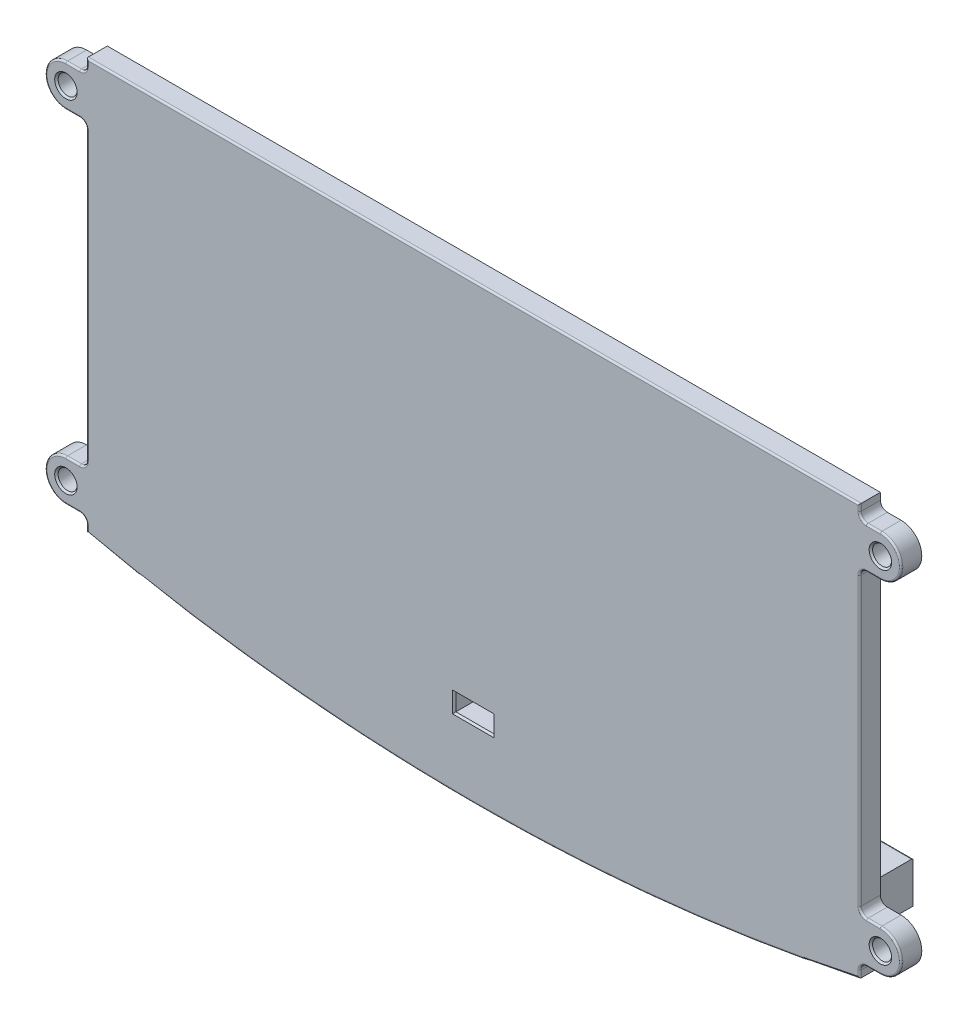
SolidWorks part; units mm, degrees
ref_plane "Front Plane" through (0, 0, 0) normal (0, 0, 1) x (1, 0, 0)
ref_plane "Top Plane" through (0, 0, 0) normal (0, 1, 0) x (1, 0, 0)
ref_plane "Right Plane" through (0, 0, 0) normal (1, 0, 0) x (0, 0, -1)
sketch "Sketch1" plane through (0, 0, 0) normal (0, 0, 1) x (1, 0, 0)
  line L5 (-56, 3) -> (56, 3)
  line L7 (56, 3) -> (56, 2)
  line L8 (57, 1) -> (59, 1)
  line L9 (59, -5) -> (57, -5)
  line L10 (56, -6) -> (56, -47.54)
  line L11 (57, -48.54) -> (59, -48.54)
  line L12 (59, -54.54) -> (57, -54.54)
  line L13 (56, -55.54) -> (56, -56.54)
  line L14 (-56, -56.54) -> (-56, -55.54)
  line L15 (-57, -54.54) -> (-59, -54.54)
  line L16 (-59, -48.54) -> (-57, -48.54)
  line L17 (-56, -47.54) -> (-56, -6)
  line L18 (-57, -5) -> (-59, -5)
  line L19 (-59, 1) -> (-57, 1)
  line L20 (-56, 2) -> (-56, 3)
  arc A13 (56, 2) -> (57, 1) centre (57, 2) ccw
  arc A14 (59, 1) -> (59, -5) centre (59, -2) cw
  arc A15 (57, -5) -> (56, -6) centre (57, -6) ccw
  arc A16 (56, -47.54) -> (57, -48.54) centre (57, -47.54) ccw construction
  arc A17 (56, -47.54) -> (57, -48.54) centre (57, -47.54) ccw
  arc A18 (59, -48.54) -> (59, -54.54) centre (59, -51.54) cw
  arc A20 (57, -54.54) -> (56, -55.54) centre (57, -55.54) ccw
  arc A21 (-56, -55.54) -> (-57, -54.54) centre (-57, -55.54) ccw
  arc A23 (-59, -54.54) -> (-59, -48.54) centre (-59, -51.54) cw
  arc A24 (-57, -48.54) -> (-56, -47.54) centre (-57, -47.54) ccw
  arc A25 (-56, -6) -> (-57, -5) centre (-57, -6) ccw
  arc A26 (-59, -5) -> (-59, 1) centre (-59, -2) cw
  arc A27 (-57, 1) -> (-56, 2) centre (-57, 2) ccw
  arc A29 (-56, -56.54) -> (56, -56.54) centre (0, 203.2465) ccw
  circle A30 centre (-59, -2) radius 1.375
  circle A31 centre (-59, -51.54) radius 1.375
  circle A32 centre (59, -51.54) radius 1.375
  circle A34 centre (59, -2) radius 1.375
  arc A35 (53, -57.1686) -> (56, -56.54) centre (0, 203.2465) ccw construction
  dimension "D1" = 2.75
extrude "Boss-Extrude1" add sketch "Sketch1" along normal blind 3
sketch "Sketch2" plane through (0, 0, 0) normal (0, 0, -1) x (-1, 0, 0)
  line L1 (54.5, -33) -> (-54.5, -33)
  line L2 (54.5, -33) -> (54.5, -30)
  line L3 (54.5, -30) -> (-54.5, -30)
  line L4 (-54.5, -33) -> (-54.5, -30)
extrude "Cut-Extrude1" cut sketch "Sketch2" against normal blind 1.5
chamfer "Chamfer1" distance 0.25 angle 45 4 edges at (60.375, -2, 3) (60.375, -51.54, 3) (-57.625, -51.54, 3) (-57.625, -2, 3)
fillet "Fillet1" radius 0.25 28 edges at (56, 2.5, 3) (56.2929, 1.2929, 3) (58, 1, 3) (62, -2, 3) (58, -5, 3) (56.2929, -5.2929, 3) (56, -26.77, 3) (56.2929, -48.2471, 3) (58, -48.54, 3) (62, -51.54, 3) (58, -54.54, 3) (56.2929, -54.8329, 3) (56, -56.04, 3) (-56, -56.04, 3) (0, -62.5072, 3) (-56.2929, -54.8329, 3) (-58, -54.54, 3) (-62, -51.54, 3) (-58, -48.54, 3) (-56.2929, -48.2471, 3) (-56, -26.77, 3) (-56.2929, -5.2929, 3) (-58, -5, 3) (-62, -2, 3) (-58, 1, 3) (-56.2929, 1.2929, 3) (-56, 2.5, 3) (0, 3, 3)
sketch "Sketch3" plane through (0, 0, 0) normal (0, 0, -1) x (-1, 0, 0)
  line L0 (53, -54.54) -> (51, -54.54) construction
  line L1 (52.75, -54.54) -> (-52.75, -54.54)
  line L2 (52.75, -54.54) -> (52.75, -48.54)
  line L3 (52.75, -48.54) -> (-52.75, -48.54)
  line L4 (-52.75, -54.54) -> (-52.75, -48.54)
  line L5 (-53, -33) -> (-53, -50.54) construction
  line L6 (53, -50.54) -> (53, -33) construction
  dimension "D1" = 0.25
  dimension "D2" = 0.25
  dimension "D3" = 6
extrude "Boss-Extrude2" add sketch "Sketch3" along normal blind 8
sketch "Sketch4" plane through (0, -54.54, 0) normal (0, -1, 0) x (1, 0, 0)
  line L0 (52.75, 0) -> (-52.75, 0) construction
  circle A0 centre (0, -3.25) radius 1.75
  point P4 (-3.4689, -3.25)
  dimension "D2" = 3.5
  dimension "D1" = 3.25
extrude "Cut-Extrude2" cut sketch "Sketch4" against normal through all
ref_plane "Plane1" through (0, -52.54, 0) normal (0, -1, 0) x (-1, 0, 0)
sketch "Sketch6" plane through (0, -52.54, 0) normal (0, -1, 0) x (-1, 0, 0)
  line L0 (2.75, 1.6623) -> (2.75, -3)
  line L1 (0, 6.4254) -> (-2.75, 4.8377)
  line L2 (-2.75, 4.8377) -> (-2.75, 1.6623)
  line L3 (-2.75, 1.6623) -> (-1.375, 0.8684) construction
  line L4 (1.375, 0.8684) -> (2.75, 1.6623) construction
  line L5 (2.75, 1.6623) -> (2.75, 4.8377)
  line L6 (2.75, 4.8377) -> (0, 6.4254)
  line L7 (-55.75, -3) -> (55.75, -3) construction
  line L8 (2.75, -3) -> (-2.75, -3)
  line L9 (-2.75, -3) -> (-2.75, 1.6623)
  line L10 (0, 0.0746) -> (1.375, 0.8684) construction
  line L11 (-1.375, 0.8684) -> (0, 0.0746) construction
  arc A0 (2.75, 3.25) -> (-2.75, 3.25) centre (0, 3.25) ccw construction
  arc A1 (-2.75, 3.25) -> (-1.375, 0.8684) centre (0, 3.25) ccw construction
  arc A2 (-1.375, 0.8684) -> (1.375, 0.8684) centre (0, 3.25) ccw construction
  arc A3 (1.375, 0.8684) -> (2.75, 3.25) centre (0, 3.25) ccw construction
  point P15 (0, 3.25)
  point P17 (-3.1371, 2.3327)
  dimension "D1" = 5.5
extrude "Cut-Extrude3" cut sketch "Sketch6" against normal blind 2.5
sketch "Sketch7" plane through (0, 0, 0) normal (0, 0, -1) x (-1, 0, 0)
  line L0 (-54.5, -33) -> (54.5, -33) construction
  line L1 (52.75, -48.54) -> (50.75, -48.54)
  line L2 (52.75, -48.54) -> (52.75, -33)
  line L3 (52.75, -33) -> (50.75, -33)
  line L4 (50.75, -48.54) -> (50.75, -33)
  line L5 (0, 5.5) -> (0, -62.5072) construction
  line L6 (52.75, -30) -> (50.75, -30)
  line L7 (52.75, -30) -> (52.75, -0.25)
  line L8 (52.75, -0.25) -> (50.75, -0.25)
  line L9 (50.75, -30) -> (50.75, -0.25)
  line L10 (55.75, 5.5) -> (-55.75, 5.5) construction
  line L11 (54.5, -30) -> (-54.5, -30) construction
  line L12 (53, 0) -> (-53, 0) construction
  line L13 (-50.75, -30) -> (-50.75, -0.25)
  line L14 (-52.75, -0.25) -> (-50.75, -0.25)
  line L15 (-52.75, -30) -> (-52.75, -0.25)
  line L16 (-52.75, -30) -> (-50.75, -30)
  line L17 (-50.75, -48.54) -> (-50.75, -33)
  line L18 (-52.75, -33) -> (-50.75, -33)
  line L19 (-52.75, -48.54) -> (-52.75, -33)
  line L20 (-52.75, -48.54) -> (-50.75, -48.54)
  arc A0 (-56, -56.54) -> (56, -56.54) centre (0, 203.2465) ccw construction
  dimension "D1" = 0.25
  dimension "D2" = 2
extrude "Boss-Extrude3" add sketch "Sketch7" along normal blind 2.5
chamfer "Chamfer2" distance 0.25 angle 45 16 edges at (52.75, -15.125, -2.5) (52.75, -40.77, -2.5) (-52.75, -40.77, -2.5) (-52.75, -15.125, -2.5) (0, -50.04, -5) (0, -50.04, 3) (2.75, -51.29, 3) (-2.75, -51.29, 3) (0, -52.54, 3) (1.75, -54.54, -3.25) (0, -30, 0) (0, -33, 0) (51.75, -30, -2.5) (51.75, -33, -2.5) (-51.75, -33, -2.5) (-51.75, -30, -2.5)
fillet "Fillet3" radius 0.25 14 edges at (-51.625, -48.54, -2.5) (-50.75, -48.54, -1.25) (51.625, -48.54, -2.5) (50.75, -48.54, -1.25) (0, -48.54, 0) (0, -48.54, -8) (50.75, -40.895, 0) (50.75, -15, 0) (50.75, -15, -2.5) (50.75, -40.895, -2.5) (-50.75, -15, -2.5) (-50.75, -15, 0) (-50.75, -40.895, 0) (-50.75, -40.895, -2.5)
